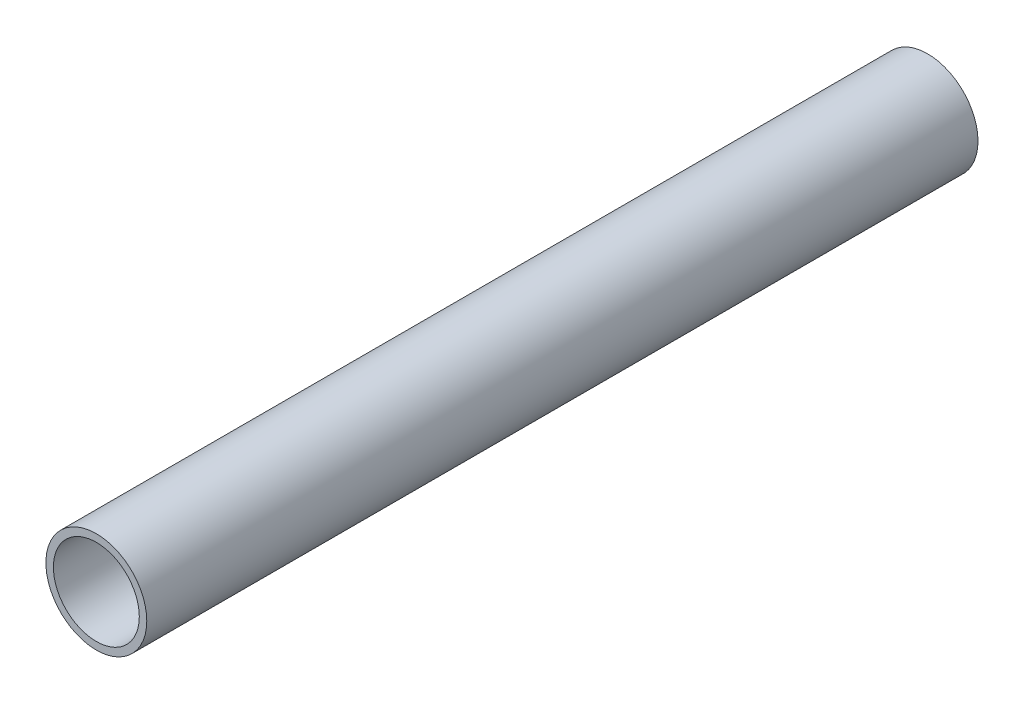
SolidWorks part; units mm, degrees
ref_plane "Front Plane" through (0, 0, 0) normal (0, 0, 1) x (1, 0, 0)
ref_plane "Top Plane" through (0, 0, 0) normal (0, 1, 0) x (1, 0, 0)
ref_plane "Right Plane" through (0, 0, 0) normal (1, 0, 0) x (0, 0, -1)
sketch "Sketch1" plane through (0, 0, 0) normal (0, 0, 1) x (1, 0, 0)
  circle A0 centre (0, 0) radius 2.7
  circle A1 centre (0, 0) radius 2.3
  dimension "D1" = 5.4
  dimension "D2" = 4.6
extrude "Boss-Extrude1" add sketch "Sketch1" along normal blind 44.5
